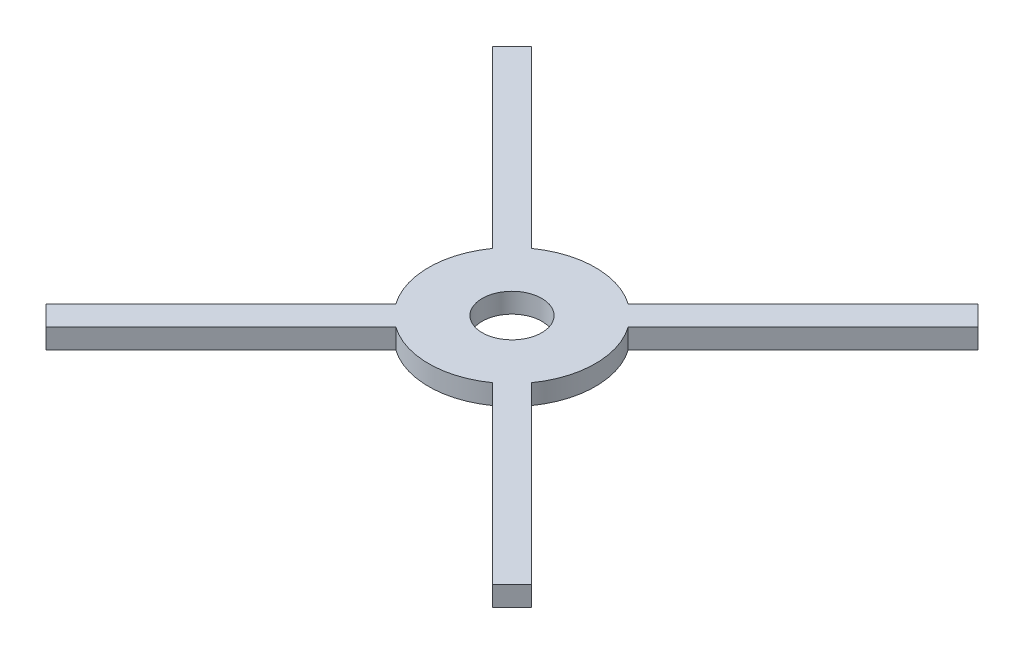
SolidWorks part; units mm, degrees
ref_plane "Спереди" through (0, 0, 0) normal (0, 0, 1) x (1, 0, 0)
ref_plane "Сверху" through (0, 0, 0) normal (0, 1, 0) x (1, 0, 0)
ref_plane "Справа" through (0, 0, 0) normal (1, 0, 0) x (0, 0, -1)
other "Configuration Table"
sketch "Эскиз1" plane through (0, 0, 0) normal (0, 1, 0) x (1, 0, 0)
  line L0 (-58.7044, -58.7044) -> (58.7044, 58.7044) construction
  line L1 (-61.1792, -56.2295) -> (56.2295, 61.1792)
  line L2 (-56.2295, -61.1792) -> (61.1792, 56.2295)
  line L3 (-58.7044, 58.7044) -> (58.7044, -58.7044) construction
  line L4 (-56.2295, 61.1792) -> (61.1792, -56.2295)
  line L5 (-61.1792, 56.2295) -> (56.2295, -61.1792)
  line L6 (-56.2295, 61.1792) -> (-61.1792, 56.2295)
  line L7 (56.2295, 61.1792) -> (61.1792, 56.2295)
  line L8 (61.1792, -56.2295) -> (56.2295, -61.1792)
  line L9 (-61.1792, -56.2295) -> (-56.2295, -61.1792)
  circle A0 centre (0, 0) radius 21
  circle A1 centre (0, 0) radius 7.5
  arc A2 (-61.1792, -56.2295) -> (-56.2295, -61.1792) centre (-58.7044, -58.7044) ccw
  arc A3 (61.1792, 56.2295) -> (56.2295, 61.1792) centre (58.7044, 58.7044) ccw
  arc A4 (-56.2295, 61.1792) -> (-61.1792, 56.2295) centre (-58.7044, 58.7044) ccw
  arc A5 (56.2295, -61.1792) -> (61.1792, -56.2295) centre (58.7044, -58.7044) ccw
  point P6 (0, 0)
  point P16 (0, 0)
  point P21 (0, 0)
  dimension "D1" = 2
extrude "Бобышка-Вытянуть1" add sketch "Эскиз1" along normal blind 5 contours A1 L4 A0 L2 | A1 L2 A0 L5 | A1 L5 A0 L1 | A1 L4 A0 L5 | A1 L1 A0 L2 | A1 L5 A0 L4 | A1 L1 A0 L4 | L2 A3 L1 A0 | A1 L2 A0 L1 | L1 A2 L2 A0 | L5 A5 L4 A0 | L4 A4 L5 A0
